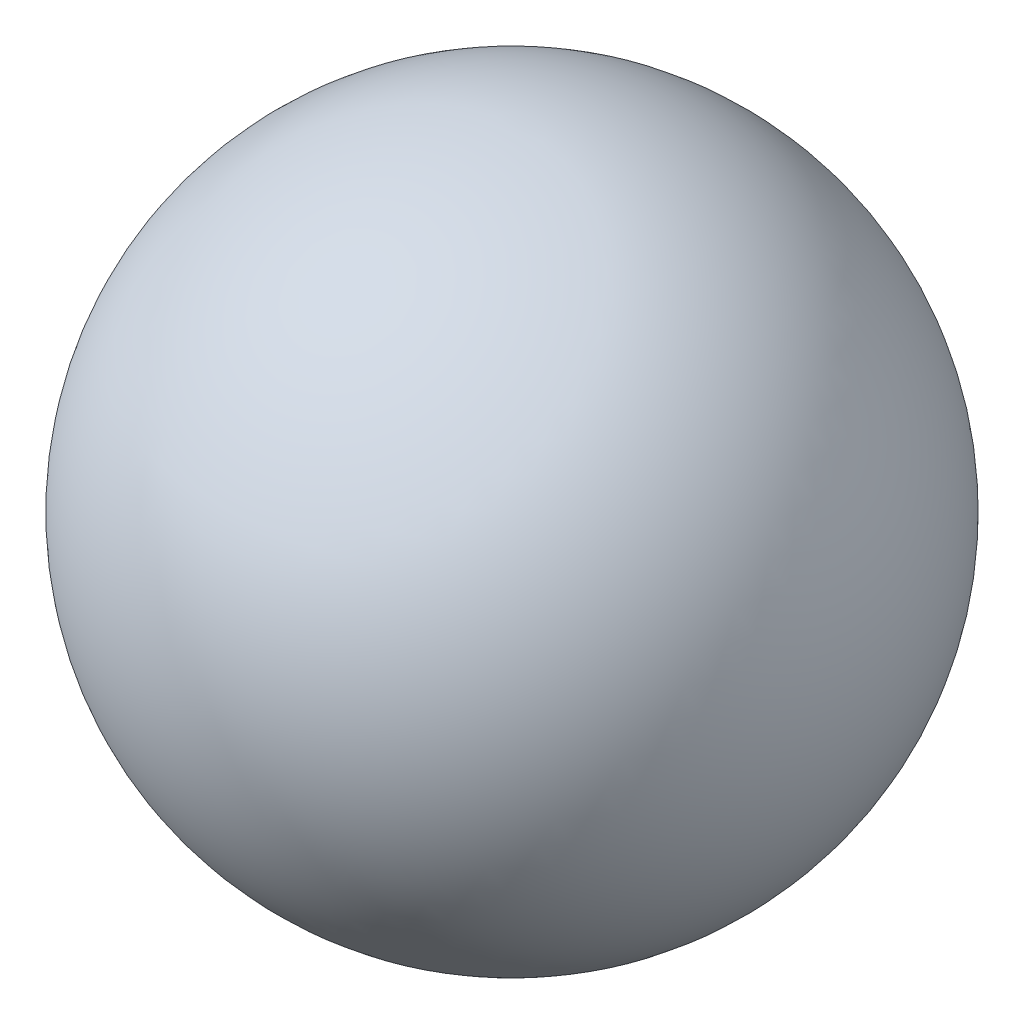
SolidWorks part; units mm, degrees
ref_plane "Front Plane" through (0, 0, 0) normal (0, 0, 1) x (1, 0, 0)
ref_plane "Top Plane" through (0, 0, 0) normal (0, 1, 0) x (1, 0, 0)
ref_plane "Right Plane" through (0, 0, 0) normal (1, 0, 0) x (0, 0, -1)
ref_axis "Axe1" through (0, -24.475, 0) along (0, 1, 0)
sketch "Esquisse1" plane through (0, 0, 0) normal (0, 0, 1) x (1, 0, 0)
  line L0 (0, -24.475) -> (0, 24.475) construction
  line L1 (0, 22.25) -> (0, -22.25)
  arc A0 (0, -22.25) -> (0, 22.25) centre (0, 0) ccw
  dimension "D1" = 22.25
revolve "Révolution1" add sketch "Esquisse1" angle 360 about axis through (0, -24.475, 0) along (0, 1, 0)
